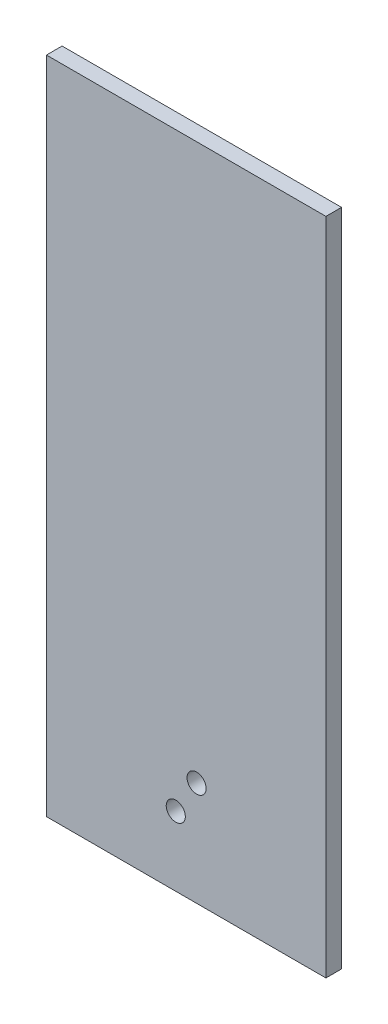
SolidWorks part; units mm, degrees
material "Perspex (TM) GS Acrylic Cast Sheet"
ref_plane "Front Plane" through (0, 0, 0) normal (0, 0, 1) x (1, 0, 0)
ref_plane "Top Plane" through (0, 0, 0) normal (0, 1, 0) x (1, 0, 0)
ref_plane "Right Plane" through (0, 0, 0) normal (1, 0, 0) x (0, 0, -1)
sketch "Sketch1" plane through (0, 0, 0) normal (0, 0, 1) x (1, 0, 0)
  line L1 (-80.5, -190) -> (80.5, -190)
  line L2 (-80.5, -190) -> (-80.5, 190)
  line L3 (-80.5, 190) -> (80.5, 190)
  line L4 (80.5, -190) -> (80.5, 190)
  line L5 (-80.5, -190) -> (80.5, 190) construction
  line L6 (-80.5, 190) -> (80.5, -190) construction
  point P0 (0, 0)
  dimension "D1" = 161
  dimension "D2" = 380
extrude "Boss-Extrude1" add sketch "Sketch1" along normal blind 9
sketch "Sketch2" plane through (0, 0, 9) normal (0, 0, 1) x (1, 0, 0)
  line L0 (6, -130) -> (6, -190) construction
  line L2 (-80.5, -190) -> (80.5, -190) construction
  line L3 (-6, -190) -> (-6, -150) construction
  circle A0 centre (6, -130) radius 5.5
  circle A1 centre (-6, -150) radius 5.5
  point P7 (0, -190)
  dimension "D1" = 11
  dimension "D2" = 60
  dimension "D3" = 6
  dimension "D4" = 6
  dimension "D5" = 40
extrude "Cut-Extrude1" cut sketch "Sketch2" against normal through all
equation "\"PCLength\"= 143mm'Length across I/O from PS to GPU"
equation "\"PCWidth\"= 340mm'Distance of longest part parallel to GPU(ussually GPU)"
equation "\"PCHeight\"= 190mm'Tallest point with mobo laying flat"
equation "\"WallThickness\"= 9mm'Thickness of each outer tank wall"
equation "\"ThermoBarrierThickness\"= 6mm'Thickness of barrier between hot side and cold side"
equation "\"HotSideGap\"= 15mm'Space in the hot side that hot fluid flows into"
equation "\"PCClearance\"= 40mm'Clearance from top of tank to top of PC"
equation "\"RadiatorHeight\"= 277.37mm'Final Height from ground of radiators"
equation "\"D1@Sketch1\"=\"PCLength\" + (2 * \"WallThickness\")"
equation "\"D2@Sketch1\"=\"PCWidth\" + \"PCClearance\""
equation "\"D1@Boss-Extrude1\"=\"WallThickness\""
